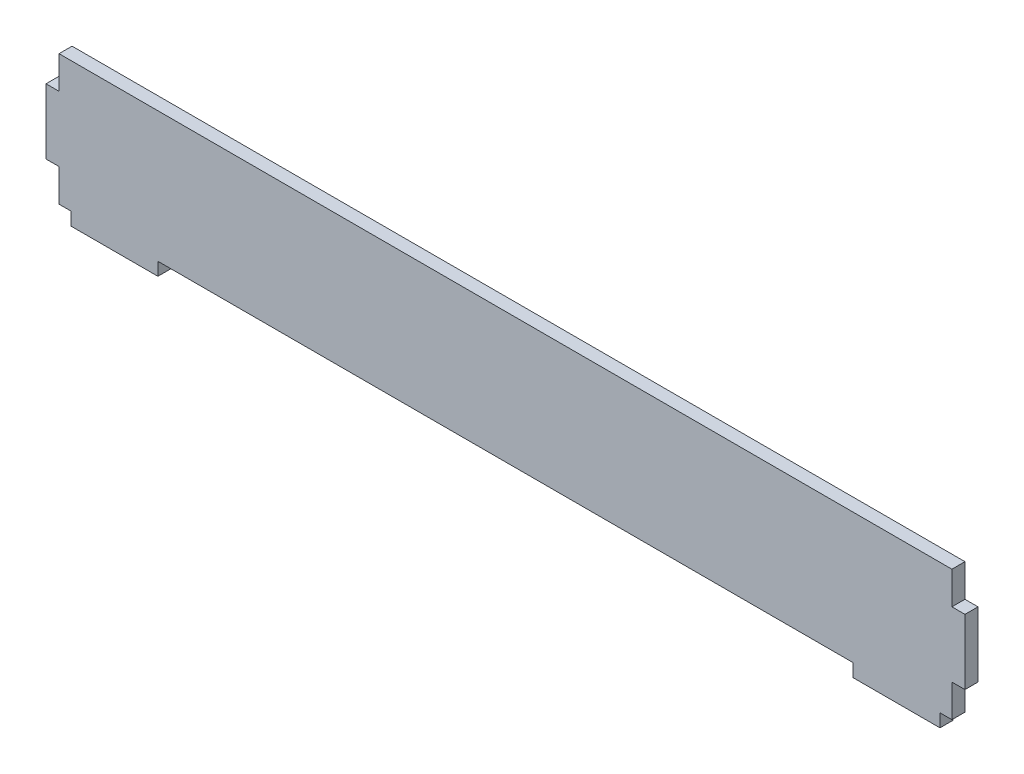
SolidWorks part; units mm, degrees
ref_plane "前视基准面" through (0, 0, 0) normal (0, 0, 1) x (1, 0, 0)
ref_plane "上视基准面" through (0, 0, 0) normal (0, 1, 0) x (1, 0, 0)
ref_plane "右视基准面" through (0, 0, 0) normal (1, 0, 0) x (0, 0, -1)
sketch "草图1" plane through (0, 0, 0) normal (0, 0, 1) x (1, 0, 0)
  line L1 (20, 0) -> (180, 0)
  line L3 (0, 30) -> (200, 30)
  line L6 (0, 0) -> (0, -3)
  line L7 (0, -3) -> (20, -3)
  line L8 (20, 0) -> (20, -3)
  line L9 (180, 0) -> (180, -3)
  line L10 (180, -3) -> (200, -3)
  line L11 (200, -3) -> (200, 0)
  line L12 (200, 30) -> (202.75, 30)
  line L13 (202.75, 30) -> (202.75, 22.5)
  line L14 (202.75, 0) -> (200, 0)
  line L18 (202.75, 7.5) -> (205.75, 7.5)
  line L19 (205.75, 7.5) -> (205.75, 22.5)
  line L20 (205.75, 22.5) -> (202.75, 22.5)
  line L21 (0, 30) -> (-2.75, 30)
  line L22 (-2.75, 30) -> (-2.75, 22.5)
  line L23 (-2.75, 0) -> (0, 0)
  line L25 (-2.75, 22.5) -> (-5.75, 22.5)
  line L26 (-5.75, 22.5) -> (-5.75, 7.5)
  line L27 (-5.75, 7.5) -> (-2.75, 7.5)
  line L28 (-2.75, 7.5) -> (-2.75, 0)
  line L29 (202.75, 7.5) -> (202.75, 0)
  point P23 (-2.75, 15)
extrude "凸台-拉伸1" add sketch "草图1" along normal blind 3
